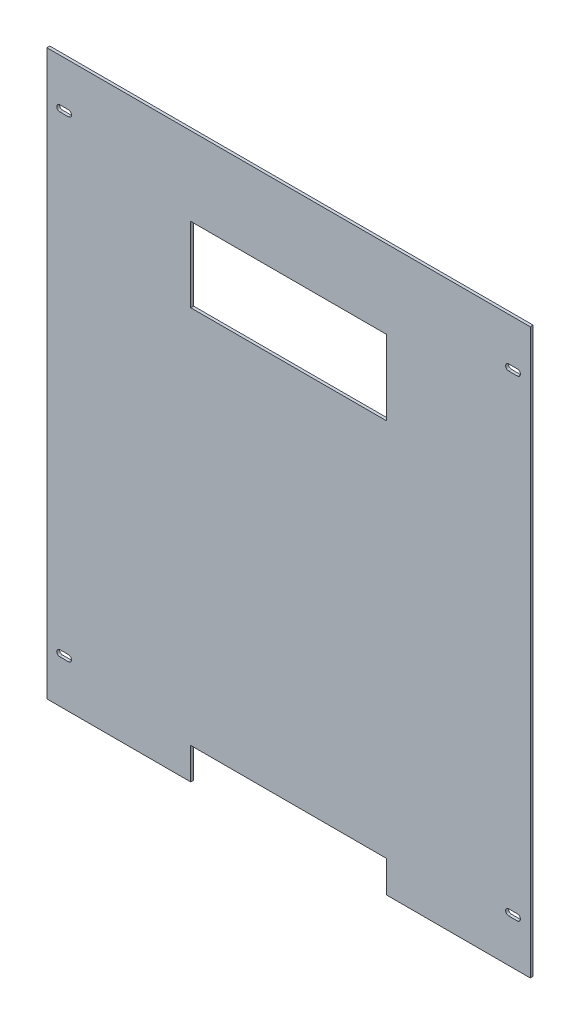
SolidWorks part; units mm, degrees
material "PC High Viscosity"
ref_plane "Front Plane" through (0, 0, 0) normal (0, 0, 1) x (1, 0, 0)
ref_plane "Top Plane" through (0, 0, 0) normal (0, 1, 0) x (1, 0, 0)
ref_plane "Right Plane" through (0, 0, 0) normal (1, 0, 0) x (0, 0, -1)
sketch "Sketch1" plane through (0, 0, 0) normal (0, 0, 1) x (1, 0, 0)
  line L0 (0, 0) -> (0, 622.3)
  line L1 (0, 0) -> (533.4, 0)
  line L2 (0, 622.3) -> (533.4, 622.3)
  line L3 (533.4, 0) -> (533.4, 622.3)
  dimension "D1" = 622.3
  dimension "D2" = 533.4
extrude "Boss-Extrude1" add sketch "Sketch1" along normal blind 3.175
sketch "Sketch2" plane through (0, 0, 3.175) normal (0, 0, 1) x (1, 0, 0)
  line L0 (14.2875, 571.5) -> (23.8125, 571.5) construction
  line L1 (14.2875, 574.8782) -> (23.8125, 574.8782)
  line L2 (14.2875, 568.1218) -> (23.8125, 568.1218)
  line L3 (0, 622.3) -> (0, 0) construction
  line L4 (533.4, 622.3) -> (0, 622.3) construction
  arc A0 (14.2875, 574.8782) -> (14.2875, 568.1218) centre (14.2875, 571.5) ccw
  arc A1 (23.8125, 568.1218) -> (23.8125, 574.8782) centre (23.8125, 571.5) ccw
  point P2 (19.05, 571.5)
  dimension "D1" = 6.7564
  dimension "D2" = 19.05
  dimension "D3" = 9.525
  dimension "D4" = 50.8
extrude "Cut-Extrude1" cut sketch "Sketch2" against normal through all
pattern_linear "LPattern1" count 2 spacing 520.7 along (0, -1, 0) count 2 spacing 495.3 along (1, 0, 0) of "Cut-Extrude1"
sketch "Sketch5" plane through (0, 0, 0) normal (0, 0, -1) x (-1, 0, 0)
  line L0 (-533.4, 0) -> (-533.4, 622.3) construction
  line L1 (-374.65, 535.697) -> (-158.75, 535.697)
  line L2 (-374.65, 535.697) -> (-374.65, 453.147)
  line L3 (-374.65, 453.147) -> (-158.75, 453.147)
  line L4 (-158.75, 535.697) -> (-158.75, 453.147)
  line L5 (-364.1725, 456.322) -> (-171.1173, 456.322) construction
  line L6 (0, 622.3) -> (0, 0) construction
  dimension "D1" = 82.55
  dimension "D2" = 215.9
  dimension "D3" = 3.175
  dimension "D4" = 158.75
  dimension "D5" = 158.75
extrude "Cut-Extrude3" cut sketch "Sketch5" against normal through all
sketch "Sketch6" plane through (0, 0, 0) normal (0, 0, -1) x (-1, 0, 0)
  line L2 (-374.65, 0) -> (-374.65, 34.925)
  line L3 (-374.65, 34.925) -> (-158.75, 34.925)
  line L4 (-158.75, 0) -> (-158.75, 34.925)
  line L9 (0, 0) -> (-533.4, 0) construction
  line L10 (-374.65, 0) -> (-158.75, 0)
  line L11 (-533.4, 0) -> (-533.4, 622.3) construction
  dimension "D1" = 158.75
  dimension "D2" = 34.925
  dimension "D3" = 34.925
  dimension "D4" = 215.9
extrude "Cut-Extrude4" cut sketch "Sketch6" against normal through all
